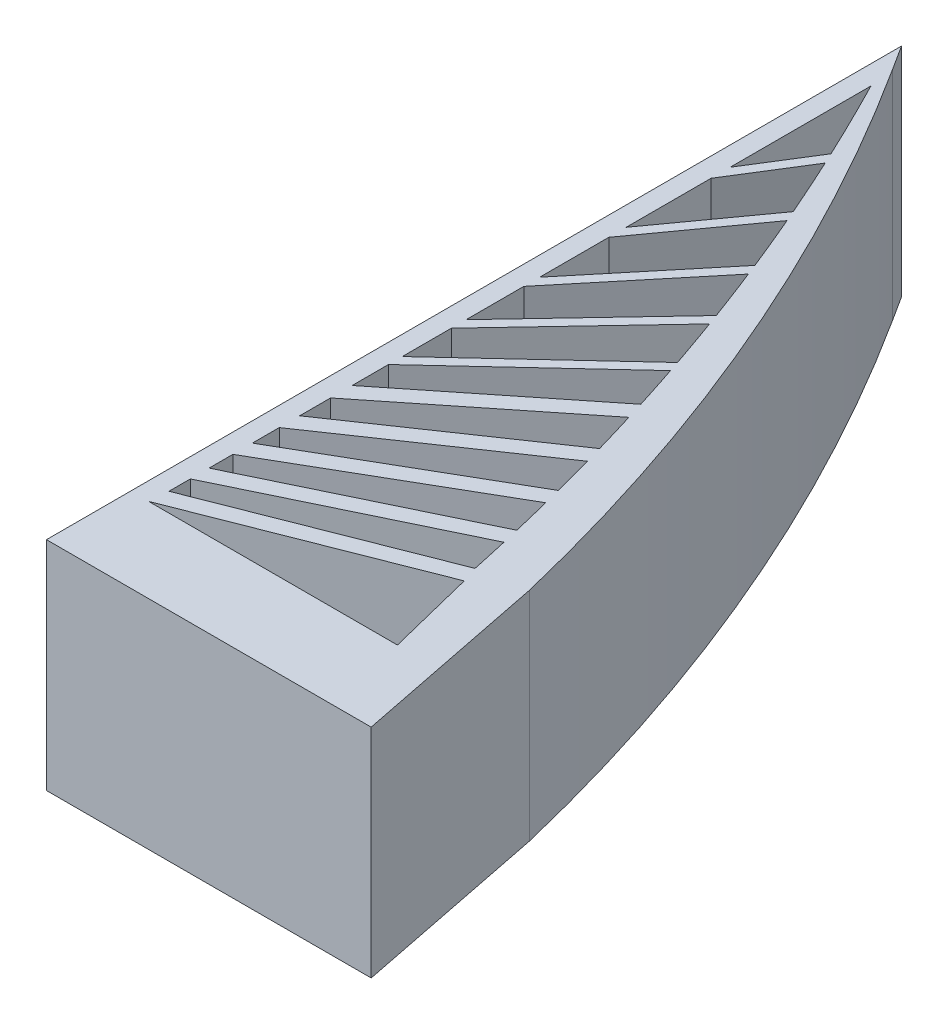
SolidWorks part; units mm, degrees
material "Rubber"
ref_plane "Front Plane" through (0, 0, 0) normal (0, 0, 1) x (1, 0, 0)
ref_plane "Top Plane" through (0, 0, 0) normal (0, 1, 0) x (1, 0, 0)
ref_plane "Right Plane" through (0, 0, 0) normal (1, 0, 0) x (0, 0, -1)
ref_plane "Plane1" through (0, -25.8, 0) normal (0, -1, 0) x (1, 0, 0)
sketch "Sketch1" plane through (0, -25.8, 0) normal (0, -1, 0) x (1, 0, 0)
  line L0 (1.6367, -33.5898) -> (31.1803, -33.5898)
  line L1 (31.1803, -33.5898) -> (28.5521, -44.1529)
  line L2 (-0.4946, -23.6898) -> (-0.4946, -23.5898)
  line L3 (-0.4946, -23.5898) -> (-0.3946, -23.5898)
  line L4 (33.9934, -23.5898) -> (38.0632, -23.5898)
  line L5 (37.2933, -27.4507) -> (38.0632, -23.5898)
  line L6 (-0.4946, -121.7004) -> (-0.4946, -125.1227)
  line L7 (-0.4946, -125.1227) -> (1.3481, -122.2388)
  line L16 (28.5521, -44.1529) -> (1.6367, -33.5898)
  line L18 (1.8, -35.8356) -> (27.9039, -46.0802)
  line L19 (26.9277, -50.484) -> (1.8, -38.3837)
  line L20 (1.8, -38.3837) -> (1.8, -35.8356)
  line L21 (1.8, -40.6035) -> (26.4619, -52.4795)
  line L22 (25.3458, -57.0255) -> (1.8, -43.4319)
  line L23 (1.8, -43.4319) -> (1.8, -40.6035)
  line L24 (1.8, -45.7413) -> (24.8276, -59.0357)
  line L25 (23.5489, -63.7642) -> (1.8, -48.9367)
  line L26 (1.8, -48.9367) -> (1.8, -45.7413)
  line L27 (1.8, -51.3573) -> (22.9742, -65.793)
  line L28 (21.5044, -70.7472) -> (1.8, -55.0343)
  line L29 (1.8, -55.0343) -> (1.8, -51.3573)
  line L30 (1.8, -57.5923) -> (20.8682, -72.7979)
  line L31 (19.1715, -78.0254) -> (1.8, -61.9076)
  line L32 (1.8, -61.9076) -> (1.8, -57.5923)
  line L33 (1.8, -63.5446) -> (18.7509, -79.2721)
  line L34 (16.6853, -85.1441) -> (1.8, -69.3794)
  line L35 (1.8, -69.3794) -> (1.8, -63.5446)
  line L36 (1.8, -71.1273) -> (16.224, -86.4034)
  line L37 (13.8664, -92.5797) -> (1.8, -77.9778)
  line L38 (1.8, -77.9778) -> (1.8, -71.1273)
  line L39 (1.8, -79.8616) -> (13.3609, -93.8518)
  line L40 (10.6622, -100.37) -> (1.8, -88.0739)
  line L41 (1.8, -88.0739) -> (1.8, -79.8616)
  line L42 (1.8, -90.1262) -> (10.1087, -101.6544)
  line L43 (7.0103, -108.5525) -> (1.8, -100.2123)
  line L44 (1.8, -100.2123) -> (1.8, -90.1262)
  line L45 (1.8, -102.4771) -> (6.4046, -109.8477)
  line L46 (1.8, -119.1977) -> (1.8, -102.4771)
  line L47 (-0.4946, -23.6898) -> (-0.4946, -121.7004)
  line L48 (33.9934, -23.5898) -> (-0.3946, -23.5898)
  arc A9 (27.9039, -46.0802) -> (26.9277, -50.484) centre (-259.6074, 15.3467) cw
  arc A10 (26.4619, -52.4795) -> (25.3458, -57.0255) centre (-259.6074, 15.3467) cw
  arc A11 (24.8276, -59.0357) -> (23.5489, -63.7642) centre (-259.6074, 15.3467) cw
  arc A12 (22.9742, -65.793) -> (21.5044, -70.7472) centre (-259.6074, 15.3467) cw
  arc A13 (20.8682, -72.7979) -> (19.1715, -78.0254) centre (-259.6074, 15.3467) cw
  arc A14 (18.7509, -79.2721) -> (16.6853, -85.1441) centre (-259.6074, 15.3467) cw
  arc A15 (16.224, -86.4034) -> (13.8664, -92.5797) centre (-259.6074, 15.3467) cw
  arc A16 (13.3609, -93.8518) -> (10.6622, -100.37) centre (-259.6074, 15.3467) cw
  arc A17 (10.1087, -101.6544) -> (7.0103, -108.5525) centre (-259.6074, 15.3467) cw
  arc A18 (6.4046, -109.8477) -> (1.8, -119.1977) centre (-259.6074, 15.3467) cw
  arc A20 (1.3481, -122.2388) -> (33.3735, -47.1078) centre (-207.3613, 11.1167) ccw
  spline S0 degree 2 poles (33.3735, -47.1078) (35.3334, -37.2792) (37.2933, -27.4507) knots 0 0 0 1 1 1
  point P1 (-0.4946, -125.1227)
  point P5 (0, 0)
  point P7 (0, 0)
  dimension "D3" = 10
extrude "Boss-Extrude1" add sketch "Sketch1" against normal blind 25.8
